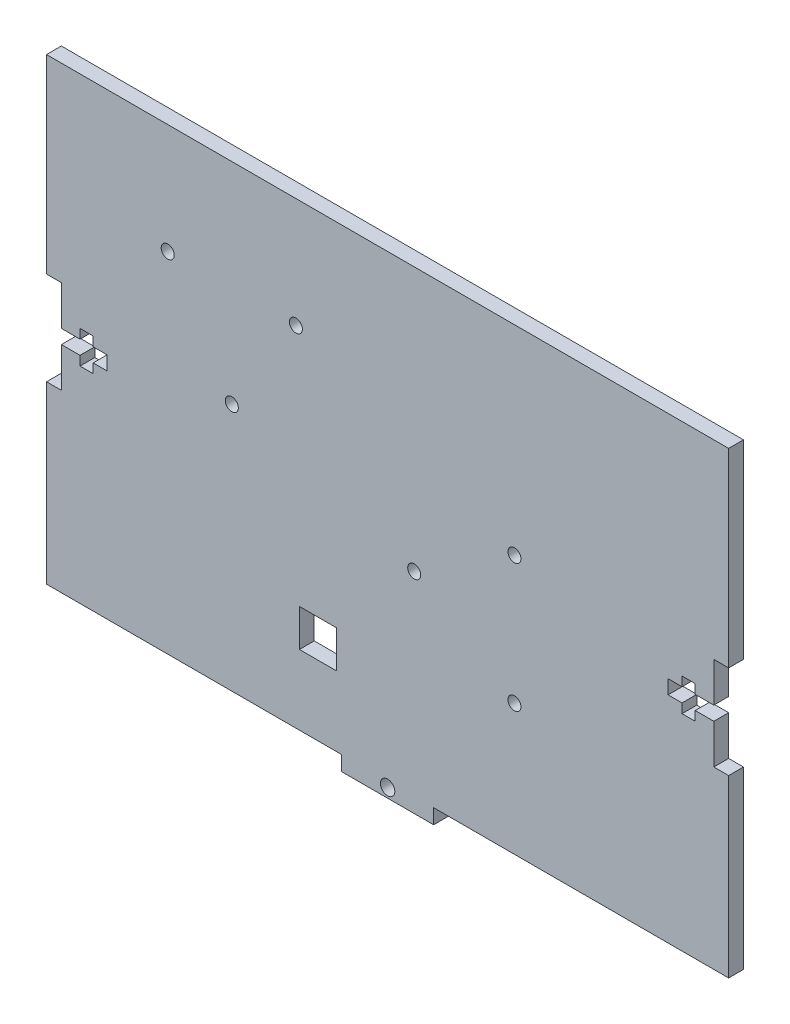
SolidWorks part; units mm, degrees
ref_plane "Front Plane" through (0, 0, 0) normal (0, 0, 1) x (1, 0, 0)
ref_plane "Top Plane" through (0, 0, 0) normal (0, 1, 0) x (1, 0, 0)
ref_plane "Right Plane" through (0, 0, 0) normal (1, 0, 0) x (0, 0, -1)
sketch "Sketch1" plane through (0, 0, 0) normal (0, 0, 1) x (1, 0, 0)
  line L1 (-73.18, 50.8) -> (73.18, 50.8)
  line L2 (-73.18, 50.8) -> (-73.18, -50.8)
  line L3 (-73.18, -50.8) -> (73.18, -50.8)
  line L4 (73.18, 50.8) -> (73.18, -50.8)
  point P0 (0, 0)
  dimension "D1" = 146.36
  dimension "D2" = 101.6
  dimension "D3" = 73.18
  dimension "D4" = 50.8
extrude "Boss-Extrude1" add sketch "Sketch1" along normal blind 3.18
sketch "Sketch2" plane through (0, 0, 3.18) normal (0, 0, 1) x (1, 0, 0)
  line L0 (0, 0) -> (50000, 0) construction
  line L1 (73.18, -50.8) -> (73.18, 50.8) construction
  line L2 (-73.18, 50.8) -> (-73.18, -50.8) construction
  line L3 (-73.18, 10) -> (-70, 10)
  line L4 (-73.18, 10) -> (-73.18, -10)
  line L5 (-73.18, -10) -> (-70, -10)
  line L6 (-70, 10) -> (-70, -10)
  line L8 (-73.18, 1.5) -> (-60.18, 1.5)
  line L9 (-73.18, 1.5) -> (-73.18, -1.5)
  line L10 (-73.18, -1.5) -> (-60.18, -1.5)
  line L11 (-60.18, 1.5) -> (-60.18, -1.5)
  line L12 (-66, 3.5) -> (-63.18, 3.5)
  line L13 (-66, 3.5) -> (-66, -3.5)
  line L14 (-66, -3.5) -> (-63.18, -3.5)
  line L15 (-63.18, 3.5) -> (-63.18, -3.5)
  point P5 (73.18, 0)
  point P20 (-70, 0)
  line M16 (-73.18, 50.8) -> (-73.18, -50.8)
  dimension "D1" = 20
  dimension "D2" = 3.18
  dimension "D3" = 10
  dimension "D4" = 1.5
  dimension "D5" = 3
  dimension "D6" = 13
  dimension "D7" = 2.82
  dimension "D8" = 7
  dimension "D9" = 3.5
  dimension "D10" = 4
extrude "Cut-Extrude1" cut sketch "Sketch2" against normal through all both and the other way through all contours L8 L6 L3 M16 | L4 L0 L6 L8 | L0 L9 L10 L6 | L10 L5 L6 M16 | L6 L0 L13 L8 | L0 L6 L10 L13 | L15 L12 L13 L8 | L13 L0 L15 L8 | L0 L13 L10 L15 | L15 L10 L13 L14 | L15 L0 L11 L8 | L0 L15 L10 L11
mirror "Mirror1" about plane through (0, 0, 0) normal (1, 0, 0) of "Cut-Extrude1"
sketch "Sketch3" plane through (0, 0, 3.18) normal (0, 0, 1) x (1, 0, 0)
  line L0 (0, 0) -> (0, -50000) construction
  line L7 (-73.18, -50.8) -> (-9.875, -50.8)
  line L8 (-73.18, -50.8) -> (-73.18, -47.62)
  line L9 (-73.18, -47.62) -> (-9.875, -47.62)
  line L10 (-9.875, -50.8) -> (-9.875, -47.62)
  dimension "D1" = 63.305
  dimension "D2" = 3.18
extrude "Cut-Extrude2" cut sketch "Sketch3" against normal through all both and the other way through all
mirror "Mirror2" about plane through (0, 0, 0) normal (1, 0, 0) of "Cut-Extrude2"
sketch "Sketch4" plane through (0, 0, 3.18) normal (0, 0, 1) x (1, 0, 0)
  line L0 (-9.875, -50.8) -> (9.875, -50.8) construction
  circle A0 centre (0, -48.8) radius 1.55
  dimension "D1" = 3.1
  dimension "D2" = 2
  dimension "D3" = 9.875
extrude "Cut-Extrude3" cut sketch "Sketch4" against normal through all both and the other way through all contours A0
sketch "Sketch8" plane through (0, 0, 0) normal (0, 0, -1) x (-1, 0, 0)
  circle A0 centre (-5.7161, -5.7953) radius 1.4
  circle A1 centre (-27.2161, 7.9547) radius 1.4
  circle A2 centre (-27.2161, -19.5453) radius 1.4
  dimension "D1" = 2.8
  dimension "D2" = 2.8
  dimension "D3" = 2.8
sketch "Sketch9" plane through (0, 0, 0) normal (0, 0, -1) x (-1, 0, 0)
  line L0 (9.875, -47.62) -> (73.18, -47.62) construction
  line L1 (18.9206, -24.62) -> (10.9206, -24.62)
  line L2 (18.9206, -24.62) -> (18.9206, -32.62)
  line L3 (18.9206, -32.62) -> (10.9206, -32.62)
  line L4 (10.9206, -24.62) -> (10.9206, -32.62)
  line L5 (73.18, -10) -> (73.18, -47.62) construction
  dimension "D1" = 8
  dimension "D2" = 8
  dimension "D3" = 15
  dimension "D4" = 54.2594
extrude "Cut-Extrude7" cut sketch "Sketch9" against normal through all both and the other way through all
extrude "Cut-Extrude8" cut sketch "Sketch8" against normal through all both and the other way through all contours A1
sketch "Sketch12" plane through (0, 0, 0) normal (0, 0, -1) x (-1, 0, 0)
  circle A0 centre (19.68, 27.2) radius 1.4
  circle A1 centre (33.43, 5.7) radius 1.4
  circle A2 centre (47.18, 27.2) radius 1.4
  dimension "D1" = 2.8
  dimension "D2" = 2.8
  dimension "D3" = 2.8
extrude "Cut-Extrude9" cut sketch "Sketch12" against normal through all both and the other way through all
